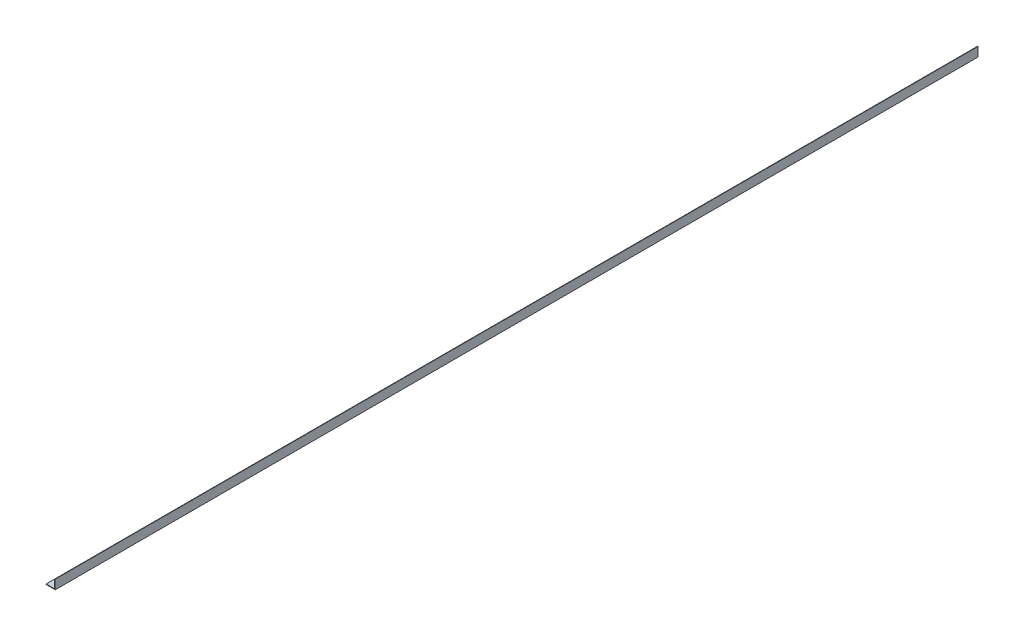
SolidWorks part; units mm, degrees
ref_plane "Front Plane" through (0, 0, 0) normal (0, 0, 1) x (1, 0, 0)
ref_plane "Top Plane" through (0, 0, 0) normal (0, 1, 0) x (1, 0, 0)
ref_plane "Right Plane" through (0, 0, 0) normal (1, 0, 0) x (0, 0, -1)
sketch "Sketch0" plane through (0, 0, 0) normal (0, 0, 1) x (1, 0, 0)
  line L0 (-12.7, -12.7) -> (12.7, -12.7)
  line L1 (12.7, -12.7) -> (12.7, 12.7)
  line L2 (12.7, 0) -> (0, 0) construction
  line L3 (0, 0) -> (0, -12.7) construction
  line L4 (11.1125, -9.5377) -> (11.1125, 12.7) construction
  line L5 (9.5377, -11.1125) -> (-12.7, -11.1125) construction
  arc A0 (11.1125, -9.5377) -> (9.5377, -11.1125) centre (9.5377, -9.5377) cw
  point P3 (10.6513, -10.6513)
  dimension "Inside Corner Radius" = 1.5748
  dimension "Outside Height" = 25.4
  dimension "Inside Height" = 23.8125
  dimension "Inside Width" = 23.8125
  dimension "Wall Thickness" = 1.5875
  dimension "D1" = 1.5875
  dimension "Outside Width" = 25.4
sketch "Sketch1" plane through (0, 0, 0) normal (1, 0, 0) x (0, 0, -1)
  line L0 (914.4, 0) -> (-914.4, 0)
  point P4 (0, 0)
  dimension "Length" = 1828.8
sketch "Sketch2" plane through (0, 0, 0) normal (0, 0, 1) x (1, 0, 0)
  line L0 (-12.7, -12.7) -> (12.7, -12.7)
  line L1 (12.7, -12.7) -> (12.7, 12.7)
  line L2 (12.7, 12.7) -> (11.1125, 12.7) construction
  line L3 (11.1125, 11.9062) -> (11.1125, -9.5377)
  line L4 (9.5377, -11.1125) -> (-11.9062, -11.1125)
  line L5 (-12.7, -12.7) -> (-12.7, -11.1125) construction
  line L6 (11.9062, 12.7) -> (12.7, 12.7)
  line L7 (-12.7, -11.9062) -> (-12.7, -12.7)
  line L8 (12.7, 0) -> (0, 0) construction
  line L9 (0, 0) -> (0, -12.7) construction
  arc A0 (11.1125, 11.9062) -> (11.9062, 12.7) centre (11.9062, 11.9062) cw
  arc A1 (-12.7, -11.9062) -> (-11.9062, -11.1125) centre (-11.9062, -11.9062) cw
  arc A2 (11.1125, -9.5377) -> (9.5377, -11.1125) centre (9.5377, -9.5377) cw
  dimension "Inside Radius" = 1.5748
  dimension "Height" = 25.4
  dimension "Width" = 25.4
  dimension "Thickness" = 1.5875
extrude "Boss-Extrude1" add sketch "Sketch2" along normal mid plane 2540
sketch "Break Locations" plane through (0, 0, 0) normal (1, 0, 0) x (0, 0, -1)
  line L0 (-1244.092, 0) -> (1244.092, 0)
  line L1 (-1270, -12.7) -> (-1270, 12.7) construction
  line L2 (1270, -12.7) -> (1270, 12.7) construction
  point P0 (-1248.41, 0)
  point P1 (1248.41, 0)
  point P10 (0, 0)
  point P11 (1244.092, 0)
  point P13 (-1244.092, 0)
  dimension "D1" = 21.59
  dimension "D2" = 21.59
  dimension "D3" = 25.908
hole_wizard "1/4-20 Tapped Hole1" positions "Sketch3" profile "Sketch4" tap size "1/4-20" standard "ANSI Inch" end condition through all
sketch "Sketch3" plane through (0, -11.1125, 0) normal (0, 1, 0) x (1, 0, 0)
  line L2 (11.1125, -1270) -> (11.1125, 1270) construction
  line L4 (9.5377, 1270) -> (-11.9062, 1270) construction
  point P0 (-1.5875, -349.504)
  point P3 (-1.5875, -349.504)
  point P11 (-1.5875, 106.172)
  point P13 (-1.5875, 1017.524)
  point P15 (-1.5875, 561.848)
  dimension "D1" = 12.7
  dimension "D2" = 252.476
  dimension "D3" = 455.676
  dimension "D4" = 455.676
  dimension "D5" = 455.676
cosmetic thread "Hole Thread1" parameters "D2"=6.35
sketch "Sketch4" plane through (-1.5875, -11.1125, 349.504) normal (1, 0, 0) x (0, 0, 1)
  line L0 (0, 0) -> (0, 1.5875)
  line L1 (0, 1.5875) -> (2.5527, 1.5875)
  line L2 (2.5527, 1.5875) -> (2.5527, 0)
  line L5 (2.5527, 0) -> (0, 0)
  line L11 (0, -6.35) -> (0, 107.95) construction
  dimension "Thru Tap Drill Dia." = 5.1054
  dimension "Thru Tap Drill Depth" = 1.5875
cosmetic thread "Hole Thread2" parameters "D2"=6.35
cosmetic thread "Hole Thread3" parameters "D2"=6.35
cosmetic thread "Hole Thread4" parameters "D2"=6.35
sketch "Sketch5" plane through (0, -11.1125, 0) normal (0, 1, 0) x (1, 0, 0)
  line L0 (-1.5875, 1057.275) -> (-1.5875, 1076.325) construction
  line L1 (-4.6355, 1057.275) -> (-4.6355, 1076.325)
  line L2 (1.4605, 1057.275) -> (1.4605, 1076.325)
  line L3 (9.5377, 1270) -> (-11.9062, 1270) construction
  line L4 (11.1125, -1270) -> (11.1125, 1270) construction
  line L5 (-1.5875, 660.4) -> (-1.5875, 641.35) construction
  line L6 (1.4605, 660.4) -> (1.4605, 641.35)
  line L7 (-4.6355, 660.4) -> (-4.6355, 641.35)
  line L8 (-321.8956, 0) -> (278.4939, 0) construction
  line L9 (-1.5875, -336.55) -> (-1.5875, -317.5) construction
  line L10 (1.4605, -336.55) -> (1.4605, -317.5)
  line L11 (-4.6355, -336.55) -> (-4.6355, -317.5)
  line L12 (-1.5875, -717.55) -> (-1.5875, -1092.2) construction
  line L13 (-4.6355, -717.55) -> (-4.6355, -1092.2)
  line L14 (1.4605, -717.55) -> (1.4605, -1092.2)
  line L15 (9.5377, -1270) -> (-11.9062, -1270) construction
  arc A0 (-4.6355, 1057.275) -> (1.4605, 1057.275) centre (-1.5875, 1057.275) ccw
  arc A1 (1.4605, 1076.325) -> (-4.6355, 1076.325) centre (-1.5875, 1076.325) ccw
  arc A2 (1.4605, 660.4) -> (-4.6355, 660.4) centre (-1.5875, 660.4) ccw
  arc A3 (-4.6355, 641.35) -> (1.4605, 641.35) centre (-1.5875, 641.35) ccw
  arc A4 (1.4605, -336.55) -> (-4.6355, -336.55) centre (-1.5875, -336.55) cw
  arc A5 (-4.6355, -317.5) -> (1.4605, -317.5) centre (-1.5875, -317.5) cw
  arc A6 (-4.6355, -717.55) -> (1.4605, -717.55) centre (-1.5875, -717.55) cw
  arc A7 (1.4605, -1092.2) -> (-4.6355, -1092.2) centre (-1.5875, -1092.2) cw
  point P2 (-1.5875, 1066.8)
  point P13 (-1.5875, 650.875)
  point P23 (-1.5875, -327.025)
  point P30 (-1.5875, -904.875)
  dimension "D1" = 3.048
  dimension "D5" = 3.048
  dimension "D2" = 19.05
  dimension "D3" = 203.2
  dimension "D4" = 12.7
  dimension "D6" = 19.05
  dimension "D7" = 609.6
  dimension "D8" = 317.5
  dimension "D9" = 177.8
extrude "Cut-Extrude1" cut sketch "Sketch5" against normal through all
equation "\"D1@Break Locations\" = .85 * \"Height@Sketch2\""
equation "\"D2@Break Locations\"=\"D1@Break Locations\""
equation "\"Thickness@Sketch2\"=\"wall thickness@sketch0\""
equation "\"Height@Sketch2\"=\"outside height@sketch0\""
equation "\"Width@Sketch2\"=\"outside width@sketch0\""
equation "\"Inside Radius@Sketch2\"=\"inside corner radius@sketch0\""
equation "\"D3@Break Locations\"=\"D2@Break Locations\"*1.2"
equation "\"D1@Sketch0\"=\"Wall Thickness@Sketch0\""
